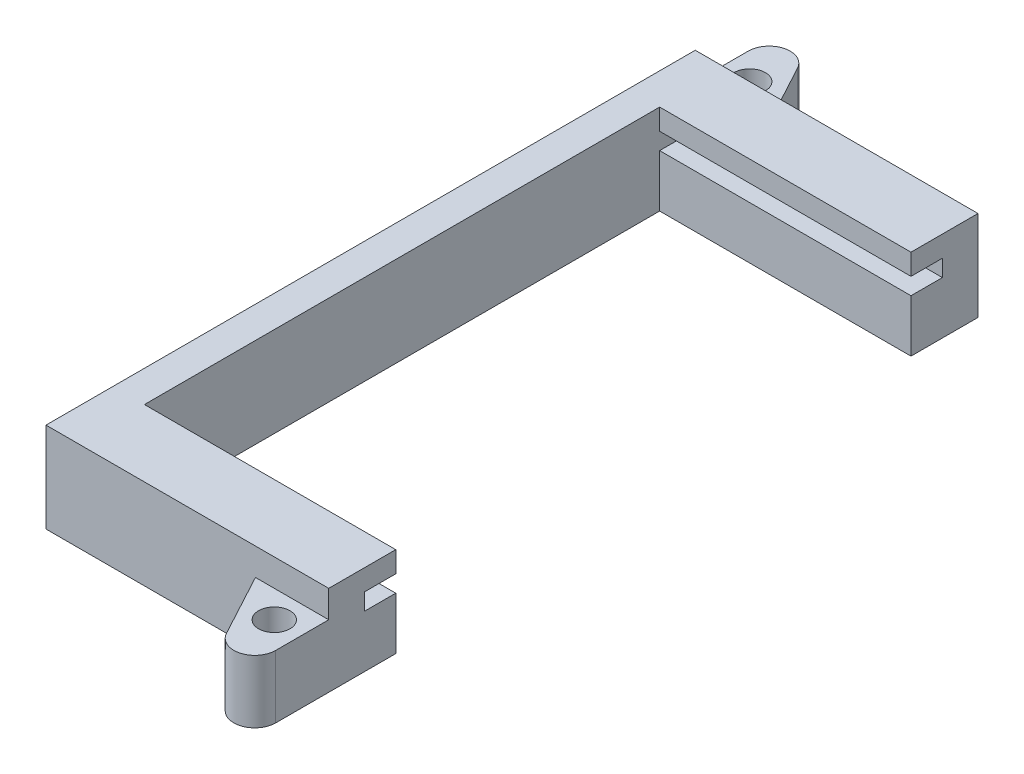
SolidWorks part; units mm, degrees
ref_plane "Front Plane" through (0, 0, 0) normal (0, 0, 1) x (1, 0, 0)
ref_plane "Top Plane" through (0, 0, 0) normal (0, 1, 0) x (1, 0, 0)
ref_plane "Right Plane" through (0, 0, 0) normal (1, 0, 0) x (0, 0, -1)
sketch "Sketch1" plane through (0, 0, 0) normal (1, 0, 0) x (0, 0, -1)
  line L0 (0, 0) -> (78.74, 0)
  line L1 (0, 0) -> (0, 10.922)
  line L2 (0, 10.922) -> (8.128, 10.922)
  line L3 (8.128, 10.922) -> (8.128, 8.382)
  line L4 (8.128, 8.382) -> (4.318, 8.382)
  line L5 (4.318, 8.382) -> (4.318, 6.35)
  line L6 (4.318, 6.35) -> (74.422, 6.35)
  line L7 (39.37, 0) -> (39.37, 24.5189) construction
  line L8 (78.74, 0) -> (78.74, 10.922)
  line L9 (74.422, 8.382) -> (74.422, 6.35)
  line L10 (70.612, 8.382) -> (74.422, 8.382)
  line L11 (70.612, 10.922) -> (70.612, 8.382)
  line L12 (78.74, 10.922) -> (70.612, 10.922)
  point P10 (39.37, 0)
  point P17 (39.37, 6.35)
  dimension "D1" = 78.74
  dimension "D2" = 2.032
  dimension "D3" = 6.35
  dimension "D4" = 2.54
  dimension "D5" = 35.052
  dimension "D6" = 3.81
extrude "Boss-Extrude1" add sketch "Sketch1" along normal blind 30.48
sketch "Sketch2" plane through (0, 0, 0) normal (0, 0, 1) x (1, 0, 0)
  line L0 (30.48, 10.922) -> (0, 10.922) construction
  line L1 (0, 0) -> (-3.81, 0)
  line L2 (0, 0) -> (0, 10.922)
  line L3 (0, 10.922) -> (-3.81, 10.922)
  line L4 (-3.81, 0) -> (-3.81, 10.922)
  dimension "D1" = 3.81
extrude "Boss-Extrude2" add sketch "Sketch2" against normal up to surface (78.74 mm away) up to face at (15.24, 5.461, -78.74)
sketch "Sketch4" plane through (0, 0, 0) normal (0, -1, 0) x (1, 0, 0)
  line L0 (21.59, 0) -> (25.7041, 7.6324)
  line L1 (30.48, 0) -> (-3.81, 0) construction
  line L2 (30.48, 0) -> (30.48, 6.4272)
  line L3 (21.59, 0) -> (30.48, 0)
  line L4 (-3.81, -78.74) -> (-3.81, -85.1672)
  line L5 (0.9659, -86.3724) -> (5.08, -78.74)
  line L6 (30.48, -78.74) -> (-3.81, -78.74) construction
  line L7 (-3.81, -78.74) -> (5.08, -78.74)
  arc A0 (25.7041, 7.6324) -> (30.48, 6.4272) centre (27.94, 6.4272) cw
  arc A1 (-3.81, -85.1672) -> (0.9659, -86.3724) centre (-1.27, -85.1672) ccw
  point P4 (28.5615, 8.89)
  point P14 (-1.8915, -87.63)
  dimension "D1" = 2.54
  dimension "D4" = 2.54
  dimension "D2" = 8.89
  dimension "D3" = 8.89
  dimension "D5" = 8.89
  dimension "D6" = 8.89
extrude "Boss-Extrude3" add sketch "Sketch4" against normal blind 7.62
sketch "Sketch5" plane through (0, 7.62, 0) normal (0, 1, 0) x (1, 0, 0)
  line L0 (5.08, 78.74) -> (-3.81, 78.74) construction
  line L1 (-3.81, 78.74) -> (-3.81, 85.1672) construction
  line L2 (21.59, 0) -> (30.48, 0) construction
  line L3 (30.48, 0) -> (30.48, -6.4272) construction
  circle A1 centre (-0.508, 82.042) radius 1.905
  circle A2 centre (27.178, -3.302) radius 1.905
  dimension "D1" = 3.81
  dimension "D4" = 3.81
  dimension "D2" = 3.302
  dimension "D3" = 3.302
  dimension "D5" = 3.302
  dimension "D6" = 3.302
extrude "Cut-Extrude2" cut sketch "Sketch5" against normal through all
sketch "Sketch6" plane through (0, 6.35, 0) normal (0, 1, 0) x (1, 0, 0)
  line L1 (0, 70.612) -> (30.48, 70.612)
  line L2 (0, 70.612) -> (0, 8.128)
  line L3 (0, 8.128) -> (30.48, 8.128)
  line L4 (30.48, 70.612) -> (30.48, 8.128)
extrude "Cut-Extrude3" cut sketch "Sketch6" against normal through all
